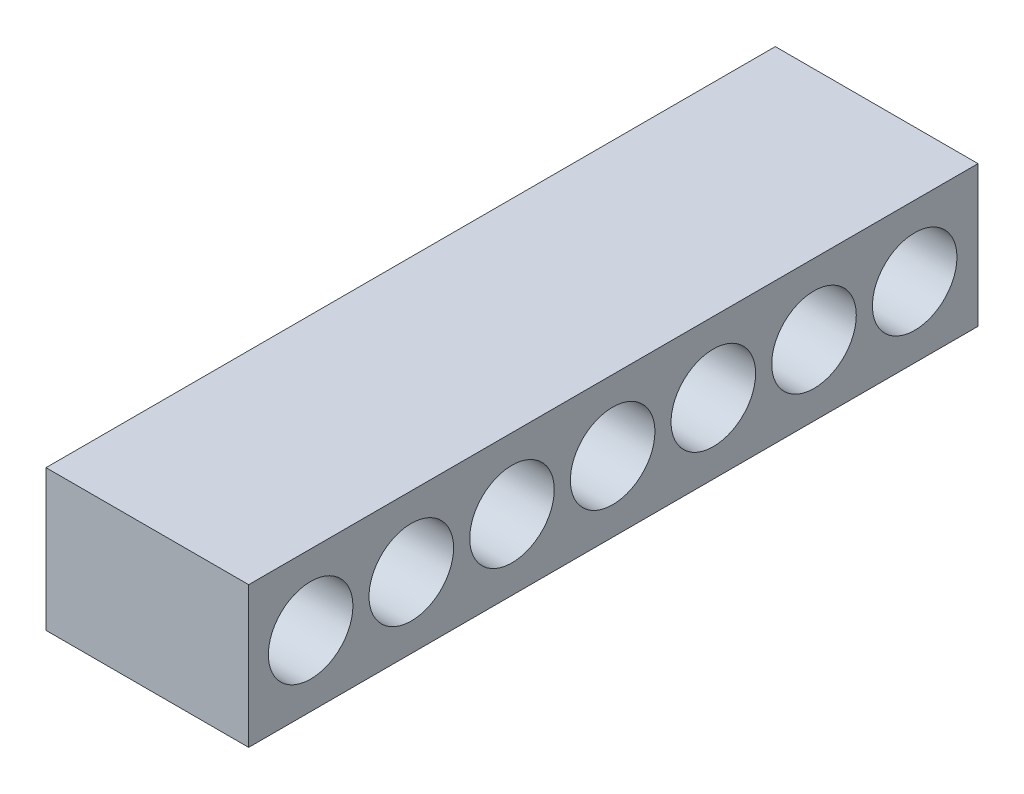
SolidWorks part; units mm, degrees
ref_plane "Front Plane" through (0, 0, 0) normal (0, 0, 1) x (1, 0, 0)
ref_plane "Top Plane" through (0, 0, 0) normal (0, 1, 0) x (1, 0, 0)
ref_plane "Right Plane" through (0, 0, 0) normal (1, 0, 0) x (0, 0, -1)
sketch "Sketch1" plane through (0, 0, 0) normal (0, 1, 0) x (1, 0, 0)
  line L1 (-1.9177, 7.5) -> (1.9177, 7.5)
  line L2 (-1.9177, 7.5) -> (-1.9177, -7.5)
  line L3 (-1.9177, -7.5) -> (1.9177, -7.5)
  line L4 (1.9177, 7.5) -> (1.9177, -7.5)
  line L5 (-1.9177, 7.5) -> (1.9177, -7.5) construction
  line L6 (-1.9177, -7.5) -> (1.9177, 7.5) construction
  point P0 (0, 0)
  dimension "D1" = 15
  dimension "D2" = 3.8354
extrude "Boss-Extrude1" add sketch "Sketch1" along normal blind 2.667
sketch "Sketch4" plane through (1.9177, 0, 0) normal (1, 0, 0) x (0, 0, -1)
  line L0 (-7.5, 1.3335) -> (7.5, 1.3335) construction
  line L1 (-7.5, 2.667) -> (-7.5, 0) construction
  line L2 (7.5, 2.667) -> (7.5, 0) construction
  circle A0 centre (-6.3281, 1.3335) radius 0.8
  circle A1 centre (-4.4231, 1.3335) radius 0.8
  circle A2 centre (-2.5181, 1.3335) radius 0.8
  circle A3 centre (-0.6131, 1.3335) radius 0.8
  circle A4 centre (1.2919, 1.3335) radius 0.8
  circle A5 centre (3.1969, 1.3335) radius 0.8
  circle A6 centre (5.1019, 1.3335) radius 0.8
  dimension "D1" = 1.6
  dimension "D2" = 1.6
  dimension "D4" = 1.6
  dimension "D6" = 1.6
  dimension "D8" = 1.6
  dimension "D10" = 1.6
  dimension "D12" = 1.6
  dimension "D3" = 1.905
  dimension "D5" = 1.905
  dimension "D7" = 1.905
  dimension "D9" = 1.905
  dimension "D11" = 1.905
  dimension "D13" = 1.905
extrude "Cut-Extrude1" cut sketch "Sketch4" against normal blind 1.9177
sketch "Sketch5" plane through (0, 0, 0) normal (1, 0, 0) x (0, 0, -1)
  circle A0 centre (-6.3281, 1.3335) radius 0.64
  circle A1 centre (-4.4231, 1.3335) radius 0.64
  circle A2 centre (-2.5181, 1.3335) radius 0.64
  circle A3 centre (-0.6131, 1.3335) radius 0.64
  circle A4 centre (1.2919, 1.3335) radius 0.64
  circle A5 centre (3.1969, 1.3335) radius 0.64
  dimension "D1" = 1.28
  dimension "D2" = 1.28
  dimension "D3" = 1.28
  dimension "D4" = 1.28
  dimension "D5" = 1.28
  dimension "D6" = 1.28
extrude "Cut-Extrude2" cut sketch "Sketch5" against normal through all
sketch "Sketch6" plane through (0, 0, 0) normal (1, 0, 0) x (0, 0, -1)
  circle A0 centre (5.1019, 1.3335) radius 0.69
  dimension "D1" = 1.38
extrude "Cut-Extrude3" cut sketch "Sketch6" against normal blind 1.27
sketch "Sketch9" plane through (0, 0, -7.5) normal (0, 0, -1) x (-1, 0, 0)
  line L1 (-1.9177, 2.667) -> (1.9177, 2.667)
  line L2 (-1.9177, 2.667) -> (-1.9177, 0)
  line L3 (-1.9177, 0) -> (1.9177, 0)
  line L4 (1.9177, 2.667) -> (1.9177, 0)
extrude "Cut-Extrude5" cut sketch "Sketch9" against normal blind 1.2
sketch "Sketch10" plane through (-1.27, 0, 0) normal (1, 0, 0) x (0, 0, -1)
